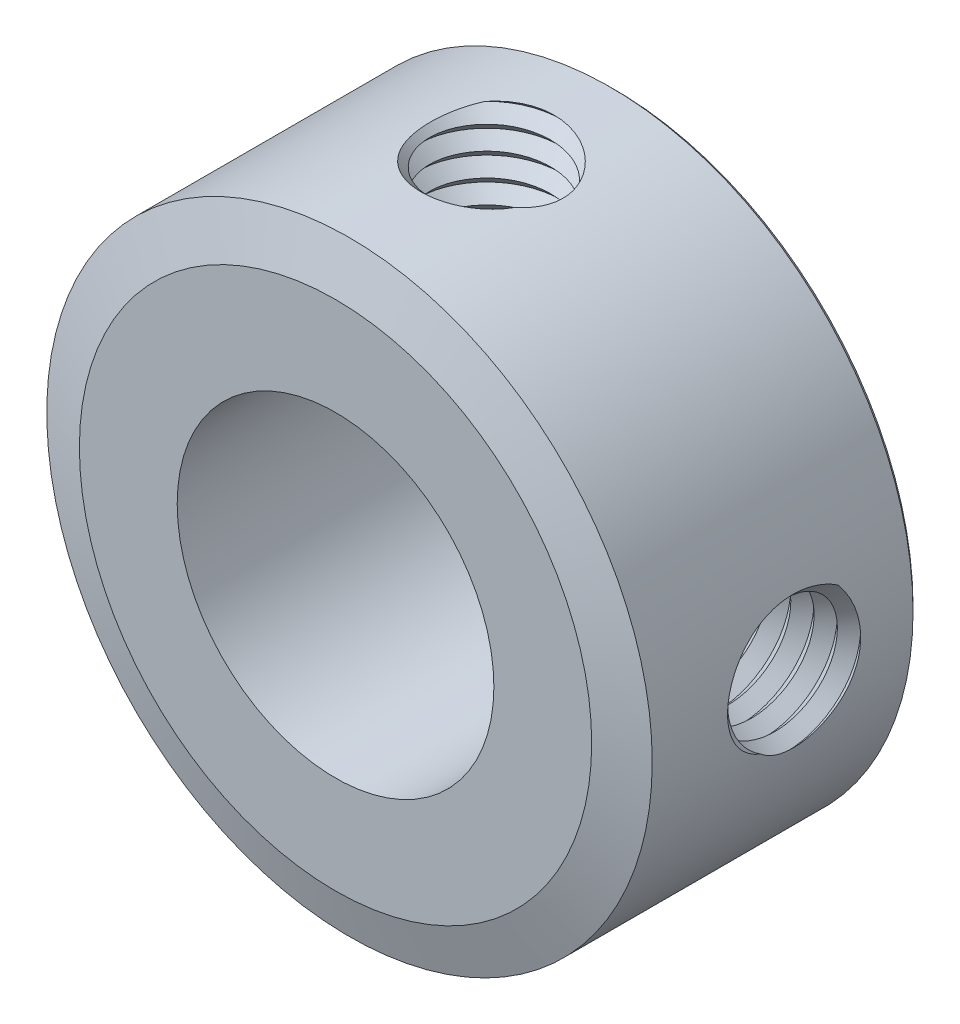
SolidWorks part; units mm, degrees
material "1060 Сплав"
ref_plane "Front Plane" through (0, 0, 0) normal (0, 0, 1) x (1, 0, 0)
ref_plane "Top Plane" through (0, 0, 0) normal (0, 1, 0) x (1, 0, 0)
ref_plane "Right Plane" through (0, 0, 0) normal (1, 0, 0) x (0, 0, -1)
sketch "Sketch1" plane through (0, 0, 0) normal (0, 0, 1) x (1, 0, 0)
  circle A0 centre (0, 0) radius 6.5
  circle A1 centre (0, 0) radius 3.4
  dimension "D1" = 13
  dimension "D2" = 6.8
extrude "Extrude1" add sketch "Sketch1" along normal blind 6
chamfer "Chamfer1" distance 0.3 distance2 1 1 edges at (6.5, 0, 6)
sketch "Sketch2" plane through (0, 0, 0) normal (0, 1, 0) x (1, 0, 0)
  line L0 (0, 0) -> (0, -6) construction
  line L1 (-5.5, -6) -> (5.5, -6) construction
  line L2 (6.5, 0) -> (-6.5, 0) construction
  circle A0 centre (0, -2.6) radius 1.25
  dimension "D1" = 2.5
  dimension "D2" = 2.6
extrude "Extrude2" cut sketch "Sketch2" along normal through all
sketch3d "3DSketch1"
  line L0 (0.0356, 6.4999, 1.3505) -> (-0.1394, 6.4985, 3.8421)
  line L1 (-0.0519, 6.4992, 2.5963) -> (-0.0519, 0.4992, 2.5963)
  line L2 (-0.0519, 0.4992, 2.5963) -> (1.0518, 0.4992, 2.5963)
  spline S0 degree 3 poles (0.1656, 6.5, 1.35) (-0.1656, 6.5, 1.35) (-0.328, 6.4935, 1.3827) (-0.6306, 6.4711, 1.5084) (-0.769, 6.4554, 1.6012) (-0.999, 6.4238, 1.8313) (-1.0921, 6.4079, 1.9704) (-1.2169, 6.3854, 2.271) (-1.2499, 6.3787, 2.4358) (-1.25, 6.3787, 2.681) (-1.2419, 6.3803, 2.764) (-1.2099, 6.3864, 2.9245) (-1.1863, 6.3909, 3.0025) (-1.0921, 6.4079, 3.2299) (-1.0003, 6.4236, 3.3674) (-0.7679, 6.4555, 3.5999) (-0.6303, 6.4711, 3.6918) (-0.3281, 6.4935, 3.8172) (-0.1639, 6.5, 3.8499) (0.1628, 6.5, 3.8501) (0.3277, 6.4935, 3.8172) (0.6287, 6.4713, 3.6926) (0.7678, 6.4555, 3.5998) (0.9984, 6.4239, 3.3695) (1.091, 6.4081, 3.2318) (1.2172, 6.3853, 2.9285) (1.2499, 6.3787, 2.766) (1.2501, 6.3787, 2.4358) (1.2174, 6.3853, 2.2727) (1.0923, 6.4079, 1.9706) (0.9994, 6.4238, 1.8318) (0.7697, 6.4553, 1.6018) (0.6306, 6.4711, 1.5085) (0.33, 6.4934, 1.3834) (0.1656, 6.5, 1.35) (-0.1656, 6.5, 1.35) (-0.328, 6.4935, 1.3827) knots -0.0625 -0.0625 0 0 0.0625 0.0625 0.125 0.125 0.1875 0.1875 0.25 0.25 0.28125 0.28125 0.3125 0.3125 0.375 0.375 0.4375 0.4375 0.5 0.5 0.5625 0.5625 0.625 0.625 0.6875 0.6875 0.75 0.75 0.8125 0.8125 0.875 0.875 0.9375 0.9375 1 1 1.0625 1.0625 1.125 only from (0, 6.5, 1.35) to (0, 6.5, 1.35) construction
sketch3d "3DSketch2"
  line L0 (-0.0519, 6.4992, 2.5963) -> (-0.0519, 0.4992, 2.5963) construction
  line L1 (-0.0519, 0.4992, 2.5963) -> (1.0518, 0.4992, 2.5963) construction
sketch "Sketch3" plane through (0, 0, 2.5963) normal (0, 0, 1) x (1, 0, 0)
  line L0 (-0.0519, 6.4992) -> (-0.0519, 6.9472) construction
  line L1 (-0.0519, 6.9472) -> (-1.5519, 6.9472) construction
  line L2 (-1.3019, 7.1972) -> (-1.5519, 6.9472)
  line L3 (-1.5519, 6.9472) -> (-1.3019, 6.6972)
  line L4 (-1.3019, 6.6972) -> (-0.7943, 6.6972)
  line L5 (-0.7943, 6.6972) -> (-0.7943, 7.1972)
  line L6 (-0.7943, 7.1972) -> (-1.3019, 7.1972)
  point P6 (-1.3384, 6.7809)
  point P9 (-1.2887, 6.7017)
  dimension "D1" = 0.5
  dimension "D2" = 45
  dimension "D3" = 1.5
  dimension "D4" = 45
sketch "Sketch5" plane through (0, 0, 0) normal (0, 1, 0) x (1, 0, 0)
  circle A0 centre (0, -2.6) radius 1.25
  dimension "D1" = 2.5
curve "Helix/Spiral1" pitch 0.5 height 8 turns 16
sweep "Cut-Sweep1" cut profiles "Sketch3" path "Helix/Spiral1"
pattern_circular "CirPattern1" count 2 over 270 about axis through (0, 0, 6) along (0, 0, -1) of "Extrude2"
pattern_circular "CirPattern2" count 2 over 90 about axis through (0, 0, 6) along (0, 0, -1) of "Cut-Sweep1"
chamfer "Chamfer2" distance 0.1 angle 45 2 edges at (3.4, 0, 0) (6.5, 0, 0)
